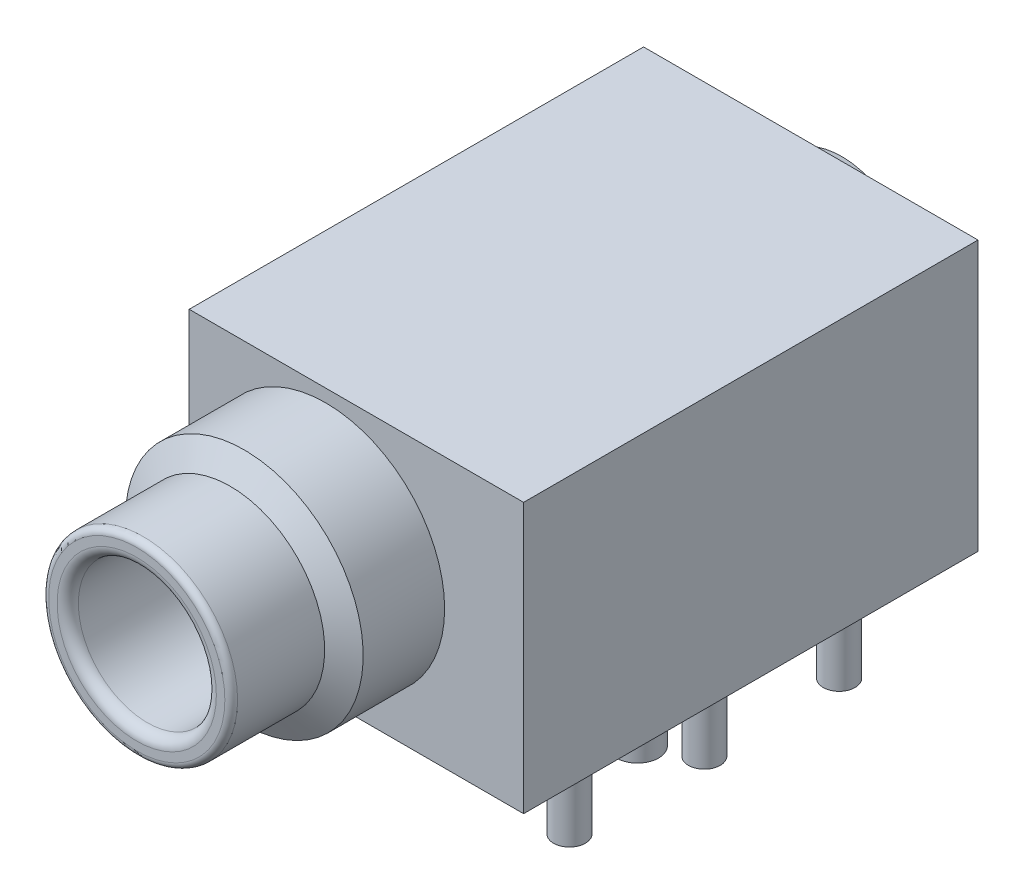
SolidWorks part; units mm, degrees
ref_plane "Front Plane" through (0, 0, 0) normal (0, 0, 1) x (1, 0, 0)
ref_plane "Top Plane" through (0, 0, 0) normal (0, 1, 0) x (1, 0, 0)
ref_plane "Right Plane" through (0, 0, 0) normal (1, 0, 0) x (0, 0, -1)
ref_plane "Plane1" through (0, 0, 0) normal (0, -1, 0) x (1, 0, 0)
sketch "Sketch1" plane through (0, 0, 0) normal (0, -1, 0) x (1, 0, 0)
  line L0 (9.32, -21.4) -> (9.32, 0)
  line L1 (9.32, 0) -> (-6.43, 0)
  line L2 (-6.43, 0) -> (-6.43, -21.4)
  line L3 (-6.43, -21.4) -> (9.32, -21.4)
extrude "Boss-Extrude1" add sketch "Sketch1" against normal blind 12.7
ref_plane "Plane2" through (0, 6.5, 0) normal (0, -1, 0) x (1, 0, 0)
sketch "Sketch2" plane through (0, 6.5, 0) normal (0, -1, 0) x (1, 0, 0)
  line L0 (4.15, -21.4) -> (0, -21.4)
  line L1 (0, -21.4) -> (0, -24.3)
  line L2 (0, -24.3) -> (3.5, -24.3)
  line L3 (3.5, -24.3) -> (4.15, -21.4)
  line L4 (0, -21.4) -> (0, -24.3) construction
revolve "Revolve1" add sketch "Sketch2" angle 360 about L4
ref_plane "Plane3" through (0, 0, -10.6) normal (0, 0, 1) x (1, 0, 0)
sketch "Sketch3" plane through (0, 0, -10.6) normal (0, 0, 1) x (1, 0, 0)
  line L0 (-3.45, 0) -> (-4.2, 0)
  line L1 (-4.2, 0) -> (-4.2, -4)
  line L2 (-4.2, -4) -> (-3.45, -4)
  line L3 (-3.45, -4) -> (-3.45, 0)
  line L4 (-4.2, 0) -> (-4.2, -4) construction
revolve "Contact Pin #1" add sketch "Sketch3" angle 360 about L4
sketch "Sketch4" plane through (0, 0, -10.6) normal (0, 0, 1) x (1, 0, 0)
  line L0 (7.98, 0) -> (7.23, 0)
  line L1 (7.23, 0) -> (7.23, -4)
  line L2 (7.23, -4) -> (7.98, -4)
  line L3 (7.98, -4) -> (7.98, 0)
  line L4 (7.23, 0) -> (7.23, -4) construction
revolve "Contact Pin #2" add sketch "Sketch4" angle 360 about L4
ref_plane "Plane4" through (0, 0, -16.95) normal (0, 0, 1) x (1, 0, 0)
sketch "Sketch5" plane through (0, 0, -16.95) normal (0, 0, 1) x (1, 0, 0)
  line L0 (-3.45, 0) -> (-4.2, 0)
  line L1 (-4.2, 0) -> (-4.2, -4)
  line L2 (-4.2, -4) -> (-3.45, -4)
  line L3 (-3.45, -4) -> (-3.45, 0)
  line L4 (-4.2, 0) -> (-4.2, -4) construction
revolve "Contact Pin #3" add sketch "Sketch5" angle 360 about L4
ref_plane "Plane5" through (0, 0, -4.25) normal (0, 0, 1) x (1, 0, 0)
sketch "Sketch6" plane through (0, 0, -4.25) normal (0, 0, 1) x (1, 0, 0)
  line L0 (-3.45, 0) -> (-4.2, 0)
  line L1 (-4.2, 0) -> (-4.2, -4)
  line L2 (-4.2, -4) -> (-3.45, -4)
  line L3 (-3.45, -4) -> (-3.45, 0)
  line L4 (-4.2, 0) -> (-4.2, -4) construction
revolve "Contact Pin #4" add sketch "Sketch6" angle 360 about L4
sketch "Sketch7" plane through (0, 0, -16.95) normal (0, 0, 1) x (1, 0, 0)
  line L0 (7.98, 0) -> (7.23, 0)
  line L1 (7.23, 0) -> (7.23, -4)
  line L2 (7.23, -4) -> (7.98, -4)
  line L3 (7.98, -4) -> (7.98, 0)
  line L4 (7.23, 0) -> (7.23, -4) construction
revolve "Contact Pin #5" add sketch "Sketch7" angle 360 about L4
sketch "Sketch8" plane through (0, 0, -4.25) normal (0, 0, 1) x (1, 0, 0)
  line L0 (7.98, 0) -> (7.23, 0)
  line L1 (7.23, 0) -> (7.23, -4)
  line L2 (7.23, -4) -> (7.98, -4)
  line L3 (7.98, -4) -> (7.98, 0)
  line L4 (7.23, 0) -> (7.23, -4) construction
revolve "Contact Pin #6" add sketch "Sketch8" angle 360 about L4
ref_plane "Plane6" through (0, 0, -13.8) normal (0, 0, 1) x (1, 0, 0)
sketch "Sketch9" plane through (0, 0, -13.8) normal (0, 0, 1) x (1, 0, 0)
  line L0 (6.6, 0) -> (5.1, 0)
  line L1 (5.1, 0) -> (5.1, -2)
  line L2 (5.1, -2) -> (6.6, -2)
  line L3 (6.6, -2) -> (6.6, 0)
  line L4 (5.1, 0) -> (5.1, -2) construction
revolve "Revolve8" add sketch "Sketch9" angle 360 about L4
ref_plane "Plane7" through (0, 0, -7.45) normal (0, 0, 1) x (1, 0, 0)
sketch "Sketch10" plane through (0, 0, -7.45) normal (0, 0, 1) x (1, 0, 0)
  line L0 (8.23, 0) -> (7.23, 0)
  line L1 (7.23, 0) -> (7.23, -2)
  line L2 (7.23, -2) -> (8.23, -2)
  line L3 (8.23, -2) -> (8.23, 0)
  line L4 (7.23, 0) -> (7.23, -2) construction
revolve "Revolve9" add sketch "Sketch10" angle 360 about L4
sketch "Sketch11" plane through (0, 0, -7.45) normal (0, 0, 1) x (1, 0, 0)
  line L0 (-3.2, 0) -> (-4.2, 0)
  line L1 (-4.2, 0) -> (-4.2, -2)
  line L2 (-4.2, -2) -> (-3.2, -2)
  line L3 (-3.2, -2) -> (-3.2, 0)
  line L4 (-4.2, 0) -> (-4.2, -2) construction
revolve "Revolve10" add sketch "Sketch11" angle 360 about L4
sketch "Sketch12" plane through (0, 6.5, 0) normal (0, -1, 0) x (1, 0, 0)
  line L0 (4.45, 8.9) -> (0, 8.9)
  line L1 (0, 8.9) -> (0, 0)
  line L2 (0, 0) -> (5.6, 0)
  line L3 (5.6, 0) -> (5.6, 3.836)
  line L4 (5.6, 3.836) -> (4.45, 4.5)
  line L5 (4.45, 4.5) -> (4.45, 8.9)
  line L6 (0, 8.9) -> (0, 0) construction
revolve "Revolve11" add sketch "Sketch12" angle 360 about L6
hole_wizard "Ø6.5 (6.5) Diameter Hole1" positions "Sketch14" profile "Sketch13" hole size "Ø6.5" standard "ANSI Metric"
sketch "Sketch14" plane through (0, 0, 8.9) normal (0, 0, 1) x (1, 0, 0)
  point P0 (0, 6.5)
sketch "Sketch13" plane through (0, 6.5, 8.9) normal (1, 0, 0) x (0, -1, 0)
  line L0 (0, 0) -> (0, 32)
  line L1 (0, 32) -> (3.25, 30.1236)
  line L2 (3.25, 30.1236) -> (3.25, 0)
  line L5 (3.25, 0) -> (0, 0)
  line L10 (0, 32) -> (-3.25, 30.1236) construction
  line L11 (0, -6.35) -> (0, 107.95) construction
  dimension "Hole Dia." = 6.5
  dimension "Hole Depth" = 30.1236
  dimension "Drill Angle" = 120
fillet "Fillet1" radius 0.3 1 edges at (-4.45, 6.5, 8.9)
fillet "Fillet2" radius 0.5 1 edges at (3.25, 6.5, 8.9)
